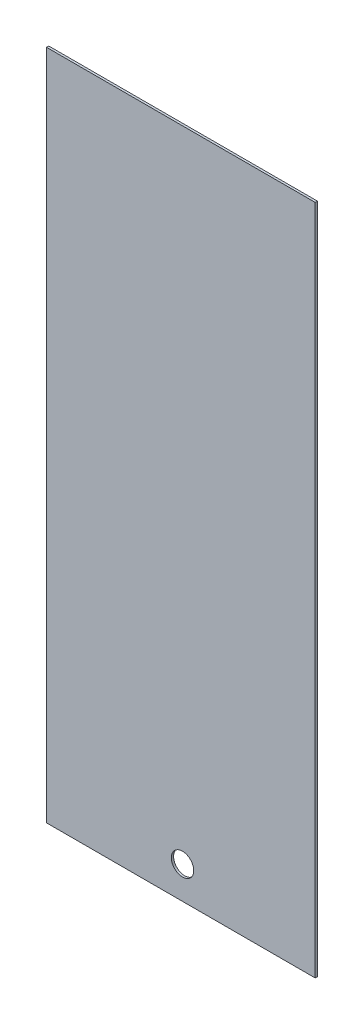
SolidWorks part; units mm, degrees
material "PVC Rigid"
ref_plane "Front Plane" through (0, 0, 0) normal (0, 0, 1) x (1, 0, 0)
ref_plane "Top Plane" through (0, 0, 0) normal (0, 1, 0) x (1, 0, 0)
ref_plane "Right Plane" through (0, 0, 0) normal (1, 0, 0) x (0, 0, -1)
sketch "Sketch1" plane through (0, 0, 0) normal (0, 0, 1) x (1, 0, 0)
  line L1 (-177.4684, 180.2538) -> (127.3316, 180.2538)
  line L2 (-177.4684, 180.2538) -> (-177.4684, -581.7462)
  line L3 (-177.4684, -581.7462) -> (127.3316, -581.7462)
  line L4 (127.3316, 180.2538) -> (127.3316, -581.7462)
  point P4 (205.3222, -124.5462)
  dimension "D1" = 762
  dimension "D2" = 304.8
extrude "Boss-Extrude1" add sketch "Sketch1" along normal blind 2.54
sketch "Sketch2" plane through (0, 0, 2.54) normal (0, 0, 1) x (1, 0, 0)
  circle A0 centre (-23.1932, -545.1629) radius 12.7
  point P2 (-26.5492, -522.3418)
  point P3 (-15.1387, -470.6587)
  point P4 (0, 0)
  point P5 (-23.8644, -581.7462)
  point P6 (-12.4538, -581.7462)
  point P7 (-23.1932, -545.1629)
  point P9 (-25.0684, -581.7462)
  dimension "D1" = 25.4
extrude "Cut-Extrude1" cut sketch "Sketch2" against normal through all
